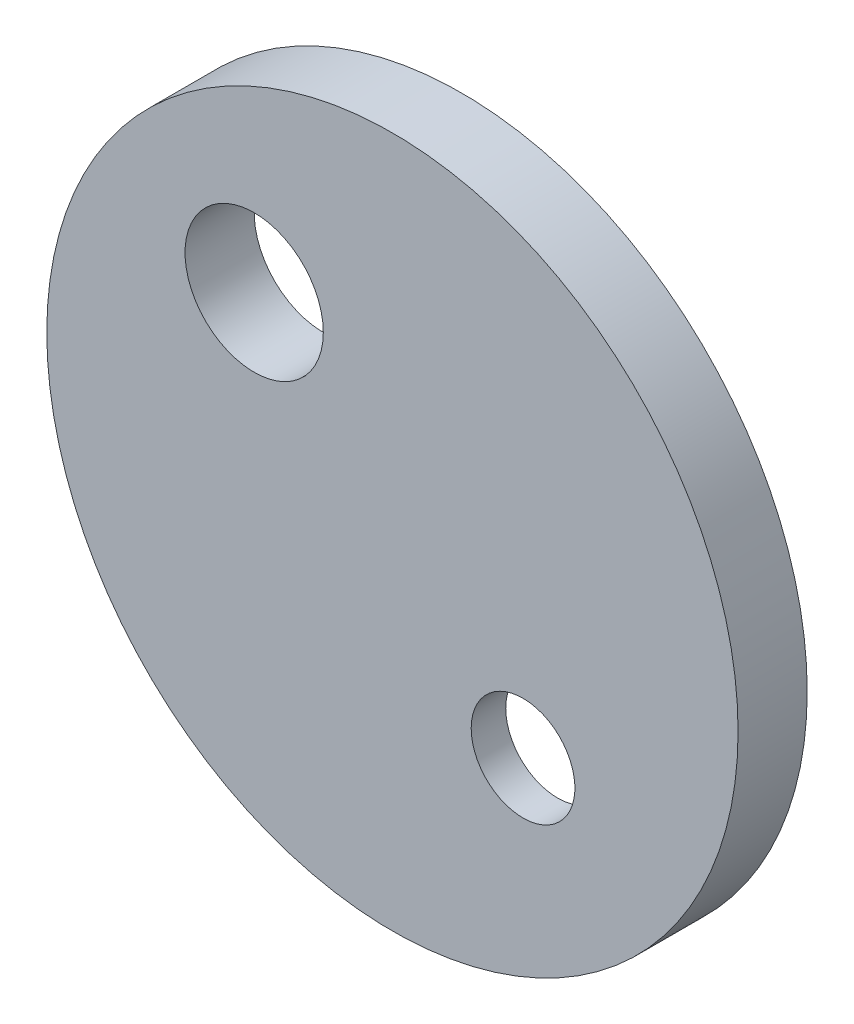
SolidWorks part; units mm, degrees
ref_plane "Alzado" through (0, 0, 0) normal (0, 0, 1) x (1, 0, 0)
ref_plane "Planta" through (0, 0, 0) normal (0, 1, 0) x (1, 0, 0)
ref_plane "Vista lateral" through (0, 0, 0) normal (1, 0, 0) x (0, 0, -1)
sketch "Croquis1" plane through (0, 0, 0) normal (0, 0, 1) x (1, 0, 0)
  circle A0 centre (0, 0) radius 2.5
  circle A1 centre (-1, 1) radius 0.5
  dimension "D1" = 5
  dimension "D4" = 1
  dimension "D2" = 1
  dimension "D3" = 1
extrude "Saliente-Extruir1" add sketch "Croquis1" along normal blind 0.5
sketch "Croquis2" plane through (0, 0, 0) normal (0, 0, -1) x (-1, 0, 0)
  line L0 (0, 0) -> (1.3841, 0) construction
  line L1 (1, 1) -> (-0.9445, -0.9445) construction
  circle A0 centre (-0.9445, -0.9445) radius 0.75
  circle A1 centre (1, 1) radius 0.5 construction
  dimension "D1" = 1.5
  dimension "D2" = 2.75
  dimension "D3" = 45
extrude "Cortar-Extruir1" cut sketch "Croquis2" against normal blind 0.25
hole_wizard "Taladro roscado M1x0.251" positions "Croquis4" profile "Croquis3" tap size "M1x0.25" standard "KS" end condition through all
sketch "Croquis4" plane through (0, 0, 0.25) normal (0, 0, -1) x (-1, 0, 0)
  circle A0 centre (-0.9445, -0.9445) radius 0.75 construction
  point P0 (-0.9445, -0.9445)
sketch "Croquis3" plane through (0.9445, -0.9445, 0.25) normal (1, 0, 0) x (0, 1, 0)
  line L0 (0, 0) -> (0, 0.25)
  line L1 (0, 0.25) -> (0.375, 0.25)
  line L2 (0.375, 0.25) -> (0.375, 0)
  line L5 (0.375, 0) -> (0, 0)
  line L11 (0, -6.35) -> (0, 107.95) construction
  dimension "Diámetro de perforador para roscar hasta el siguiente" = 0.75
  dimension "Profundidad de perforador para roscar hasta el siguiente" = 0.25
cosmetic thread "Rosca de taladro1" parameters "D2"=1
